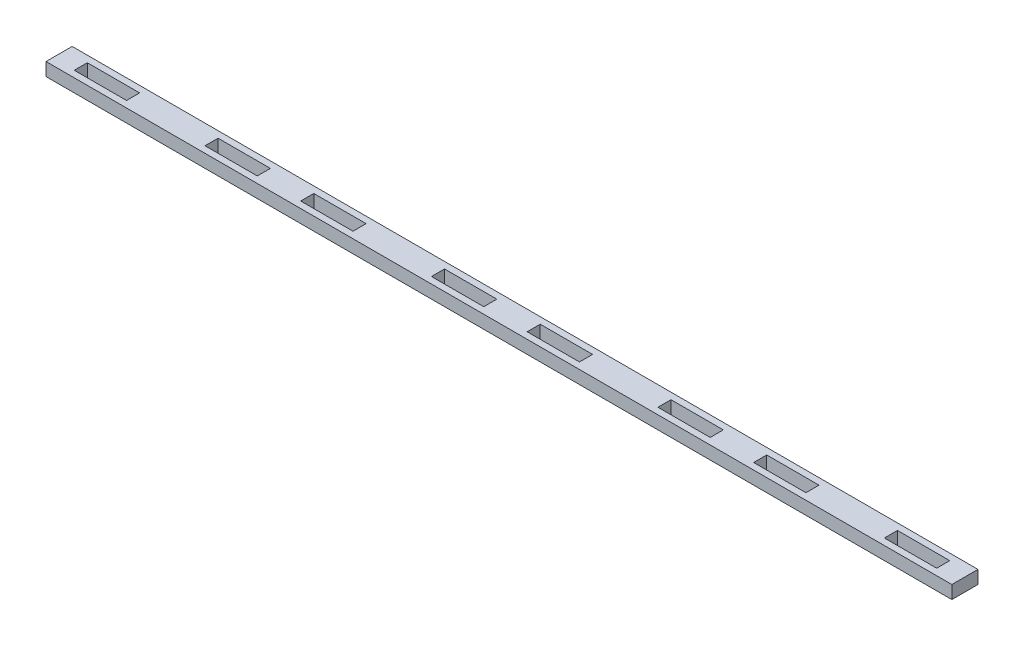
SolidWorks part; units mm, degrees
material "Cedar"
ref_plane "Front Plane" through (0, 0, 0) normal (0, 0, 1) x (1, 0, 0)
ref_plane "Top Plane" through (0, 0, 0) normal (0, 1, 0) x (1, 0, 0)
ref_plane "Right Plane" through (0, 0, 0) normal (1, 0, 0) x (0, 0, -1)
sketch "Sketch1" plane through (0, 0, 0) normal (0, 1, 0) x (1, 0, 0)
  line L1 (-219.9705, 6.35) -> (219.9705, 6.35)
  line L2 (-219.9705, 6.35) -> (-219.9705, -6.35)
  line L3 (-219.9705, -6.35) -> (219.9705, -6.35)
  line L4 (219.9705, 6.35) -> (219.9705, -6.35)
  line L5 (-219.9705, 6.35) -> (219.9705, -6.35) construction
  line L6 (-219.9705, -6.35) -> (219.9705, 6.35) construction
  point P0 (0, 0)
  dimension "D1" = 439.9409
  dimension "D2" = 12.7
extrude "Boss-Extrude1" add sketch "Sketch1" along normal blind 6.35
sketch "Sketch2" plane through (0, 6.35, 0) normal (0, 1, 0) x (1, 0, 0)
  line L0 (-23.2426, 0) -> (23.2426, 0) construction
  line L1 (-35.9426, 3.175) -> (-10.5426, 3.175)
  line L2 (-35.9426, 3.175) -> (-35.9426, -3.175)
  line L3 (-35.9426, -3.175) -> (-10.5426, -3.175)
  line L4 (-10.5426, 3.175) -> (-10.5426, -3.175)
  line L5 (-35.9426, 3.175) -> (-10.5426, -3.175) construction
  line L6 (-35.9426, -3.175) -> (-10.5426, 3.175) construction
  line L7 (10.5426, 3.175) -> (35.9426, 3.175)
  line L8 (10.5426, 3.175) -> (10.5426, -3.175)
  line L9 (10.5426, -3.175) -> (35.9426, -3.175)
  line L10 (35.9426, 3.175) -> (35.9426, -3.175)
  line L11 (10.5426, 3.175) -> (35.9426, -3.175) construction
  line L12 (10.5426, -3.175) -> (35.9426, 3.175) construction
  line L13 (-74.0426, 0) -> (-35.9426, 0) construction
  line L14 (-99.4426, 3.175) -> (-74.0426, 3.175)
  line L15 (-99.4426, 3.175) -> (-99.4426, -3.175)
  line L16 (-99.4426, -3.175) -> (-74.0426, -3.175)
  line L17 (-74.0426, 3.175) -> (-74.0426, -3.175)
  line L18 (-99.4426, 3.175) -> (-74.0426, -3.175) construction
  line L19 (-99.4426, -3.175) -> (-74.0426, 3.175) construction
  line L20 (74.0426, 3.175) -> (99.4426, 3.175)
  line L21 (74.0426, 3.175) -> (74.0426, -3.175)
  line L22 (74.0426, -3.175) -> (99.4426, -3.175)
  line L23 (99.4426, 3.175) -> (99.4426, -3.175)
  line L24 (74.0426, 3.175) -> (99.4426, -3.175) construction
  line L25 (74.0426, -3.175) -> (99.4426, 3.175) construction
  line L26 (35.9426, 0) -> (74.0426, 0) construction
  point P0 (-23.2426, 0)
  point P5 (23.2426, 0)
  point P12 (0, 0)
  point P13 (86.7426, 0)
  point P16 (-86.7426, 0)
  dimension "D1" = 46.4852
  dimension "D2" = 25.4
  dimension "D3" = 25.4
  dimension "D4" = 6.35
  dimension "D5" = 6.35
  dimension "D6" = 6.35
  dimension "D7" = 25.4
  dimension "D8" = 38.1
  dimension "D9" = 25.4
  dimension "D10" = 6.35
  dimension "D11" = 38.1
extrude "Cut-Extrude1" cut sketch "Sketch2" against normal through all
pattern_linear "LPattern1" count 2 spacing 219.9705 along (1, 0, 0) count 2 spacing 219.9705 along (-1, 0, 0) of "Cut-Extrude1"
